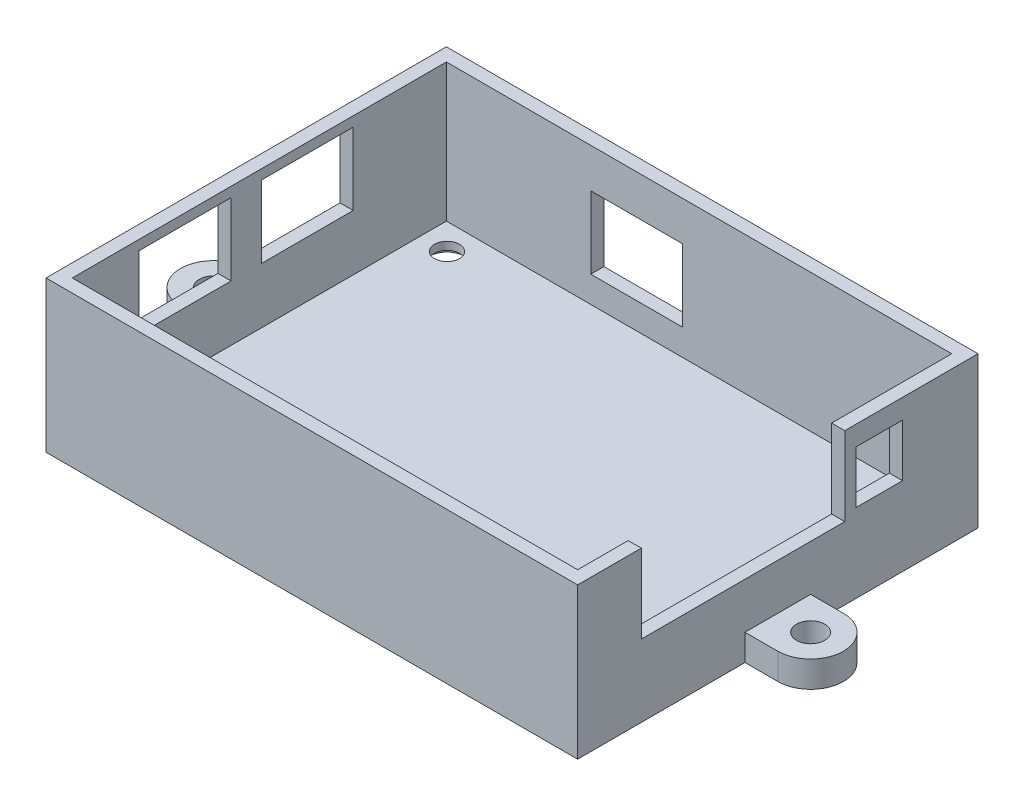
SolidWorks part; units mm, degrees
ref_plane "前视基准面" through (0, 0, 0) normal (0, 0, 1) x (1, 0, 0)
ref_plane "上视基准面" through (0, 0, 0) normal (0, 1, 0) x (1, 0, 0)
ref_plane "右视基准面" through (0, 0, 0) normal (1, 0, 0) x (0, 0, -1)
sketch "草图1" plane through (0, 0, 0) normal (0, 1, 0) x (1, 0, 0)
  line L0 (40.5, 30.5) -> (-40.5, 30.5)
  line L1 (38.5, -28.5) -> (-38.5, -28.5) construction
  line L2 (38.5, -28.5) -> (38.5, 28.5) construction
  line L3 (38.5, 28.5) -> (-38.5, 28.5) construction
  line L4 (-38.5, -28.5) -> (-38.5, 28.5) construction
  line L5 (38.5, -28.5) -> (-38.5, 28.5) construction
  line L6 (38.5, 28.5) -> (-38.5, -28.5) construction
  line L7 (-40.5, -30.5) -> (-40.5, 30.5)
  line L8 (40.5, -30.5) -> (-40.5, -30.5)
  line L9 (40.5, -30.5) -> (40.5, 30.5)
  point P0 (0, 0)
  dimension "D1" = 57
  dimension "D2" = 77
  dimension "D3" = 2
extrude "凸台-拉伸1" add sketch "草图1" along normal blind 23
shell "抽壳1" thickness 2
sketch "草图2" plane through (0, 0, 0) normal (0, -1, 0) x (1, 0, 0)
  line L0 (-40.5, -30.5) -> (-40.5, 30.5) construction
  line L1 (-40, 0) -> (40.5, 0) construction
  line L2 (40.5, 30.5) -> (40.5, -30.5) construction
  line L3 (-45.5, 5) -> (-40.5, 5)
  line L4 (-40.5, 5) -> (-40.5, -5)
  line L5 (-40.5, -5) -> (-45.5, -5)
  line L6 (0, 30.5) -> (0, -30.5) construction
  line L7 (-40.5, 30.5) -> (40.5, 30.5) construction
  line L8 (40.5, -30.5) -> (-40.5, -30.5) construction
  line L9 (40.5, -5) -> (45.5, -5)
  line L10 (40.5, 5) -> (40.5, -5)
  line L11 (45.5, 5) -> (40.5, 5)
  arc A0 (-45.5, 5) -> (-45.5, -5) centre (-45.5, 0) ccw
  circle A1 centre (-45.5, 0) radius 2.15
  circle A2 centre (45.5, 0) radius 2.15
  arc A3 (45.5, 5) -> (45.5, -5) centre (45.5, 0) cw
  point P2 (-40.5, 0)
  dimension "D1" = 10
  dimension "D3" = 4.3
  dimension "D2" = 5
extrude "凸台-拉伸3" add sketch "草图2" against normal blind 4
sketch "草图3" plane through (0, 0, 0) normal (0, 1, 0) x (1, 0, 0)
  line L1 (34.45, 24.55) -> (-34.45, 24.55) construction
  line L2 (34.45, 24.55) -> (34.45, -24.55) construction
  line L3 (34.45, -24.55) -> (-34.45, -24.55) construction
  line L4 (-34.45, 24.55) -> (-34.45, -24.55) construction
  line L5 (0, -24.55) -> (0, 24.55) construction
  line L6 (34.45, 0) -> (-34.45, 0) construction
  circle A0 centre (-34.45, -24.55) radius 1.9
  circle A1 centre (-34.45, 24.55) radius 1.9
  circle A2 centre (34.45, 24.55) radius 1.9
  circle A3 centre (34.45, -24.55) radius 1.9
  point P0 (0, 0)
  dimension "D1" = 68.9
  dimension "D2" = 49.1
extrude "切除-拉伸1" cut sketch "草图3" along normal blind 2
sketch "草图4" plane through (0, 0, 0) normal (0, 1, 0) x (1, 0, 0)
  line L1 (34.45, 24.55) -> (-34.45, 24.55) construction
  line L2 (34.45, 24.55) -> (34.45, -24.55) construction
  line L3 (34.45, -24.55) -> (-34.45, -24.55) construction
  line L4 (-34.45, 24.55) -> (-34.45, -24.55) construction
  line L5 (0, -24.55) -> (0, 24.55) construction
  line L6 (34.45, 0) -> (-34.45, 0) construction
  circle A0 centre (-34.45, -24.55) radius 2.7
  circle A1 centre (-34.45, 24.55) radius 2.7
  circle A2 centre (34.45, 24.55) radius 2.7
  circle A3 centre (34.45, -24.55) radius 2.7
  circle A4 centre (-34.45, -24.55) radius 1.9
  circle A5 centre (-34.45, 24.55) radius 1.9
  circle A6 centre (34.45, 24.55) radius 1.9
  circle A7 centre (34.45, -24.55) radius 1.9
  point P0 (0, 0)
  dimension "D1" = 68.9
  dimension "D2" = 49.1
extrude "切除-拉伸2" cut sketch "草图4" along normal blind 0.8
sketch "草图5" plane through (40.5, 0, 0) normal (1, 0, 0) x (0, 0, -1)
  line L0 (-30.417, 8) -> (30.5184, 8) construction
  line L2 (-30.5, 0) -> (-5, 0) construction
  line L3 (-30.5, 23) -> (30.5, 23) construction
  line L4 (10.2, 23) -> (-20.8, 23)
  line L5 (10.2, 23) -> (10.2, 11)
  line L6 (10.2, 11) -> (-20.8, 11)
  line L7 (-20.8, 23) -> (-20.8, 11)
  line L8 (-30.5, 23) -> (-30.5, 0) construction
  line L9 (30.5, 23) -> (30.5, 0) construction
  line L10 (19, 20) -> (11.9, 20)
  line L11 (19, 20) -> (19, 12)
  line L12 (19, 12) -> (11.9, 12)
  line L13 (11.9, 20) -> (11.9, 12)
  point P8 (-0.4653, 8)
  point P9 (-0.4653, 8)
  point P10 (-0.4653, 8)
  point P11 (-0.4653, 8)
  point P13 (-0.4653, 8)
  point P14 (-0.4653, 8)
  point P15 (-0.4653, 8)
  point P16 (-0.4653, 8)
  dimension "D1" = 8
  dimension "D2" = 3
  dimension "D3" = 0
  dimension "D4" = 31
  dimension "D5" = 9.7
  dimension "D6" = 7.1
  dimension "D7" = 8
  dimension "D8" = 4
  dimension "D9" = 11.5
extrude "切除-拉伸3" cut sketch "草图5" against normal blind 2
sketch "草图6" plane through (0, 0, -30.5) normal (0, 0, -1) x (-1, 0, 0)
  line L0 (-40.4002, 8) -> (40.4124, 8) construction
  line L1 (-40.5, 0) -> (40.5, 0) construction
  line L2 (40.5, 23) -> (40.5, 0) construction
  line L3 (16.5, 17) -> (2.5, 17)
  line L4 (16.5, 17) -> (16.5, 6)
  line L5 (16.5, 6) -> (2.5, 6)
  line L6 (2.5, 17) -> (2.5, 6)
  dimension "D1" = 8
  dimension "D2" = 14
  dimension "D3" = 11
  dimension "D4" = 2
  dimension "D5" = 24
extrude "切除-拉伸4" cut sketch "草图6" against normal blind 2
sketch "草图7" plane through (-40.5, 0, 0) normal (-1, 0, 0) x (0, 0, 1)
  line L0 (-29.91, 8) -> (30.2143, 8) construction
  line L1 (-30.5, 0) -> (-5, 0) construction
  line L2 (30.5, 23) -> (30.5, 0) construction
  line L3 (18.3, 21.5) -> (4.3, 21.5)
  line L4 (18.3, 21.5) -> (18.3, 10.5)
  line L5 (18.3, 10.5) -> (4.3, 10.5)
  line L6 (4.3, 21.5) -> (4.3, 10.5)
  line L7 (-0.3, 21.5) -> (-14.3, 21.5)
  line L8 (-0.3, 21.5) -> (-0.3, 10.5)
  line L9 (-0.3, 10.5) -> (-14.3, 10.5)
  line L10 (-14.3, 21.5) -> (-14.3, 10.5)
  line L11 (-30.5, 23) -> (-30.5, 0) construction
  dimension "D1" = 8
  dimension "D2" = 14
  dimension "D3" = 11
  dimension "D4" = 14
  dimension "D5" = 11
  dimension "D6" = 2.5
  dimension "D7" = 2.5
  dimension "D8" = 12.2
  dimension "D9" = 16.2
extrude "切除-拉伸5" cut sketch "草图7" against normal blind 2
